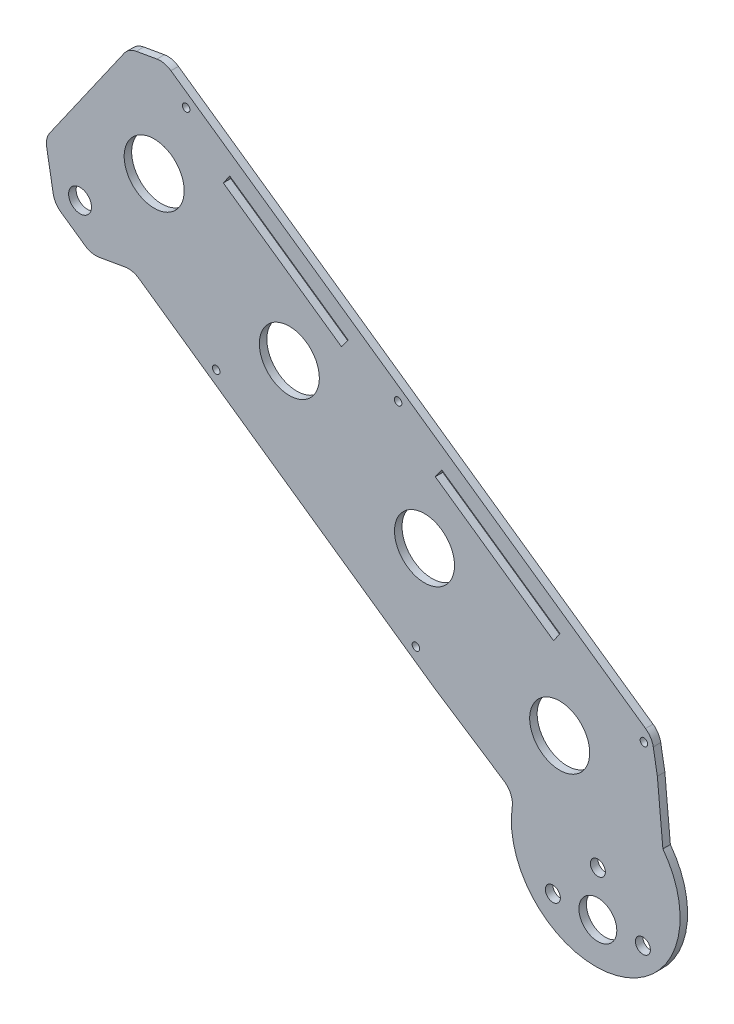
SolidWorks part; units mm, degrees
ref_plane "前视基准面" through (0, 0, 0) normal (0, 0, 1) x (1, 0, 0)
ref_plane "上视基准面" through (0, 0, 0) normal (0, 1, 0) x (1, 0, 0)
ref_plane "右视基准面" through (0, 0, 0) normal (1, 0, 0) x (0, 0, -1)
sketch "草图1" plane through (0, 0, 0) normal (0, 0, 1) x (1, 0, 0)
  line L0 (-58.5613, 85.7177) -> (-68.1414, 84.0291)
  line L1 (-68.1414, 84.0291) -> (-96.0851, 44.1269)
  line L2 (71.376, -5.2779) -> (75.1456, -26.6644)
  line L3 (71.376, -5.2779) -> (-58.5613, 85.7177)
  line L4 (-83.6508, 58.3959) -> (-39.4512, 121.5107) construction
  line L5 (-96.0851, 44.1269) -> (-78.0646, 31.507)
  line L6 (-67.0649, 33.4459) -> (32.3995, -36.2095)
  line L7 (46.3954, -69.6959) -> (68.3299, -38.3745) construction
  line L8 (51.5222, -62.375) -> (62.4212, -46.8118) construction
  line L9 (-13.9089, 50.165) -> (75.6752, -12.5712) construction
  line L10 (56.9717, -54.5934) -> (36.5587, -40.2981) construction
  line L11 (-78.0646, 31.507) -> (-67.0649, 33.4459)
  circle A0 centre (32.8778, -30.4402) radius 1 construction
  circle A3 centre (56.9717, -54.5934) radius 5.05
  circle A4 centre (-81.0978, 42.4295) radius 3.05
  arc A11 (32.3995, -36.2095) -> (75.1456, -26.6644) centre (56.4006, -43.206) ccw
  arc A14 (-68.1414, 84.0291) -> (-67.0649, 33.4459) centre (-83.6508, 58.3959) ccw construction
  dimension "D1" = 10.1
  dimension "D7" = 22
  dimension "D9" = 135
  dimension "D10" = 45
  dimension "D11" = 2
  dimension "D12" = 5.9633
  dimension "D13" = 33.5907
  dimension "D14" = 2
  dimension "D17" = 6.1
  dimension "D18" = 25
  dimension "D19" = 23.7721
  dimension "D20" = 180
  dimension "D23" = 29.9599
  dimension "D3" = 9.5
  dimension "D4" = 9.5
  dimension "D6" = 45.15
  dimension "D8" = 8.7849
  dimension "D15" = 0.2721
  dimension "D16" = 168.75
  dimension "D21" = 7.0157
  dimension "D22" = 44.1867
  dimension "D26" = 45
extrude "凸台-拉伸1" add sketch "草图1" along normal blind 2
sketch "草图4" plane through (0, 0, 2) normal (0, 0, 1) x (1, 0, 0)
  line L0 (6.4073, 40.2199) -> (-20.9516, 1.1526) construction
  line L1 (71.376, -5.2779) -> (-58.5613, 85.7177) construction
  line L2 (-67.0649, 33.4459) -> (32.3995, -36.2095) construction
  line L3 (-127.5981, 104.951) -> (113.6033, -63.9634) construction
  circle A0 centre (-61.3337, 58.5458) radius 8
  circle A1 centre (-25.2927, 33.3061) radius 8
  circle A2 centre (10.7484, 8.0664) radius 8
  circle A3 centre (46.7894, -17.1733) radius 8
  point P8 (-7.2721, 20.6862)
  dimension "D2" = 16
  dimension "D3" = 16
  dimension "D4" = 22
  dimension "D5" = 22
  dimension "D6" = 44
  dimension "D7" = 44
  dimension "D8" = 16
  dimension "D9" = 16
  dimension "D1" = 90
extrude "切除-拉伸2" cut sketch "草图4" against normal blind 10
chamfer "倒角4" distance 10 angle 45 1 edges at (-96.0851, 44.1269, 1)
fillet "圆角1" radius 5 8 edges at (32.3995, -36.2095, 1) (71.376, -5.2779, 1) (-67.0649, 33.4459, 1) (-78.0646, 31.507, 1) (-87.894, 38.3906, 1) (-90.3488, 52.318, 1) (-68.1414, 84.0291, 1) (-58.5613, 85.7177, 1)
sketch "草图5" plane through (0, 0, 0) normal (0, 0, -1) x (-1, 0, 0)
  line L0 (-90.1861, -54.5934) -> (-16.867, -54.5934) construction
  line L1 (-56.9717, -29.753) -> (-56.9717, -83.9879) construction
  circle A0 centre (-56.9717, -54.5934) radius 12
  circle A1 centre (-56.9717, -42.5934) radius 2
  circle A2 centre (-44.9717, -54.5934) radius 2
  circle A3 centre (-68.9717, -54.5934) radius 2
  dimension "D1" = 24
  dimension "D2" = 4
  dimension "D3" = 4
  dimension "D4" = 4
extrude "切除-拉伸3" cut sketch "草图5" against normal blind 10 contours A0 A1 | A0 A1 | A0 A3 | A0 A3 | A0 A2 | A0 A2
sketch "草图6" plane through (0, 0, 2) normal (0, 0, 1) x (1, 0, 0)
  line L0 (-76.0332, 94.2908) -> (80.5984, -15.3989) construction
  line L1 (-96.4101, 57.6589) -> (37.4298, -36.0697) construction
  line L3 (69.6796, -4.0899) -> (-56.8649, 84.5297) construction
  line L4 (-65.3684, 32.2578) -> (29.6585, -34.2899) construction
  line L5 (-69.3295, 82.3326) -> (-89.1608, 54.0145) construction
  circle A0 centre (-52.8107, 78.028) radius 1
  circle A1 centre (3.7082, 38.4476) radius 1
  circle A2 centre (69.2374, -7.4428) radius 1
  circle A3 centre (-44.7824, 21.5039) radius 1
  circle A4 centre (8.46, -15.782) radius 1
  dimension "D3" = 2
  dimension "D4" = 16
  dimension "D5" = 2
  dimension "D6" = 2
  dimension "D7" = 165
  dimension "D9" = 2
  dimension "D10" = 2
  dimension "D12" = 65
  dimension "D1" = 3
  dimension "D2" = 3
  dimension "D8" = 85
  dimension "D11" = 55
extrude "切除-拉伸4" cut sketch "草图6" against normal blind 10
sketch "草图7" plane through (0, 0, 0) normal (0, 0, -1) x (-1, 0, 0)
  line L0 (42.0401, 66.8228) -> (10.5042, 44.7381) construction
  line L1 (42.9005, 65.5942) -> (11.3646, 43.5094)
  line L2 (41.1797, 68.0515) -> (9.6437, 45.9668)
  line L3 (-69.6796, -4.0899) -> (56.8649, 84.5297) construction
  line L4 (42.9005, 65.5942) -> (41.1797, 68.0515)
  line L5 (11.3646, 43.5094) -> (9.6437, 45.9668)
  line L6 (52.8107, 78.028) -> (-3.7082, 38.4476) construction
  line L7 (24.5513, 58.2378) -> (15.0535, 71.8002) construction
  line L8 (24.5513, 58.2378) -> (33.2586, 45.8041) construction
  line L9 (-3.7082, 38.4476) -> (-22.6723, 65.5274) construction
  line L10 (-46.0147, 5.1577) -> (-14.4788, 27.2424) construction
  line L11 (-45.1543, 3.929) -> (-13.6184, 26.0137)
  line L12 (-46.8752, 6.3863) -> (-15.3393, 28.4711)
  line L13 (-15.3393, 28.4711) -> (-13.6184, 26.0137)
  line L14 (-46.8752, 6.3863) -> (-45.1543, 3.929)
  arc A0 (42.9005, 65.5942) -> (41.1797, 68.0515) centre (42.0401, 66.8228) ccw
  arc A1 (9.6437, 45.9668) -> (11.3646, 43.5094) centre (10.5042, 44.7381) ccw
  arc A2 (-45.1543, 3.929) -> (-46.8752, 6.3863) centre (-46.0147, 5.1577) cw
  arc A3 (-15.3393, 28.4711) -> (-13.6184, 26.0137) centre (-14.4788, 27.2424) cw
  point P2 (26.2721, 55.7805)
  point P20 (-30.2468, 16.2)
  point P30 (9.2755, 43.8777)
  dimension "D3" = 40
  dimension "D1" = 3
  dimension "D2" = 6
extrude "切除-拉伸5" cut sketch "草图7" against normal blind 10 contours L5 L1 L4 L2 | L12 L14 L11 L13
sketch "草图8" plane through (0, 0, 2) normal (0, 0, 1) x (1, 0, 0)
  line L0 (31.9299, -35.0602) -> (13.4835, -22.9625)
  line L1 (-65.3684, 32.2578) -> (29.6585, -34.2899) construction
  line L2 (72.8327, -13.5425) -> (74.3058, -29.5805)
  line L3 (75.1456, -26.6644) -> (71.7355, -7.3176) construction
  line L4 (13.4835, -22.9625) -> (28.3255, -95.0183)
  line L5 (28.3255, -95.0183) -> (121.0989, -54.0254)
  line L6 (121.0989, -54.0254) -> (72.8327, -13.5425)
  arc A0 (34.1356, -39.9621) -> (74.3058, -29.5805) centre (56.4006, -43.206) ccw
  arc A2 (31.7254, -39.1889) -> (75.1456, -26.6644) centre (56.4006, -43.206) ccw construction
  arc A3 (31.9299, -35.0602) -> (34.1356, -39.9621) centre (29.1879, -39.2413) cw
  dimension "D1" = 45
  dimension "D2" = 5
extrude "切除-拉伸6" cut sketch "草图8" against normal through all
